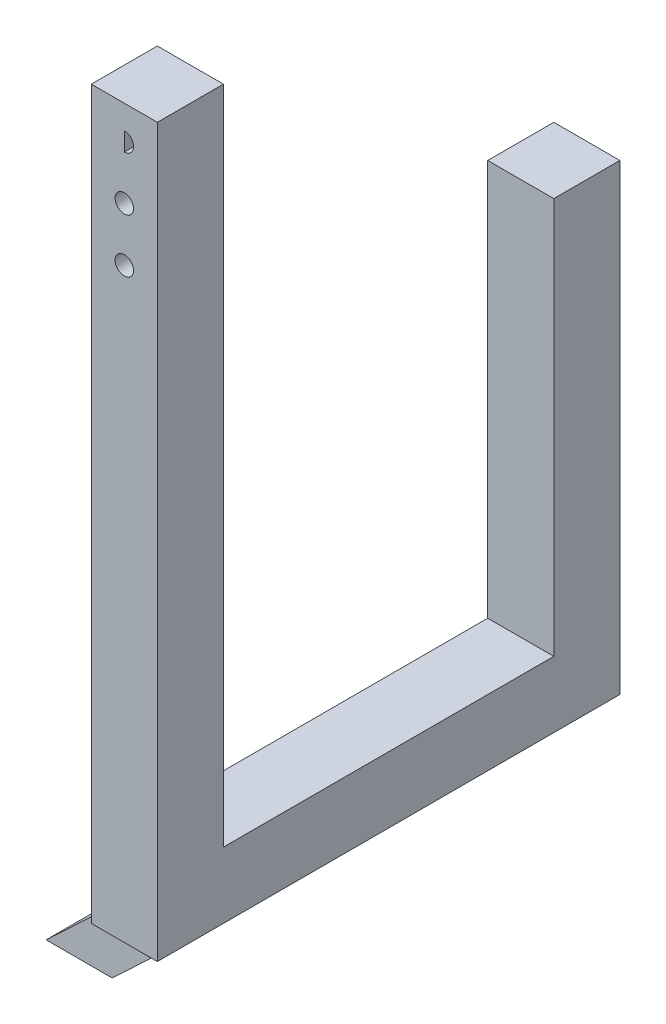
SolidWorks part; units mm, degrees
ref_plane "Front Plane" through (0, 0, 0) normal (0, 0, 1) x (1, 0, 0)
ref_plane "Top Plane" through (0, 0, 0) normal (0, 1, 0) x (1, 0, 0)
ref_plane "Right Plane" through (0, 0, 0) normal (1, 0, 0) x (0, 0, -1)
sketch "Sketch1" plane through (0, 0, 0) normal (0, 0, 1) x (1, 0, 0)
  line L1 (0, 0) -> (12.7, 0)
  line L2 (0, 0) -> (0, 139.7)
  line L3 (0, 139.7) -> (12.7, 139.7)
  line L4 (12.7, 0) -> (12.7, 139.7)
  dimension "D1" = 12.7
  dimension "D2" = 139.7
extrude "Boss-Extrude1" add sketch "Sketch1" along normal blind 12.7 contours L2 L1 L4 L3
sketch "Sketch2" plane through (0, 0, 0) normal (-1, 0, 0) x (0, 0, 1)
  line L1 (0, 0) -> (-63.5, 0)
  line L2 (0, 0) -> (0, 12.7)
  line L3 (0, 12.7) -> (-63.5, 12.7)
  line L4 (-63.5, 0) -> (-63.5, 12.7)
  dimension "D1" = 63.5
  dimension "D2" = 12.7
extrude "Boss-Extrude2" add sketch "Sketch2" against normal blind 12.7 contours L2 L1 L4 L3
sketch "Sketch3" plane through (0, 0, 0) normal (-1, 0, 0) x (0, 0, 1)
  line L1 (-63.5, 0) -> (-76.2, 0)
  line L2 (-63.5, 0) -> (-63.5, 88.9)
  line L3 (-63.5, 88.9) -> (-76.2, 88.9)
  line L4 (-76.2, 0) -> (-76.2, 88.9)
  dimension "D1" = 12.7
  dimension "D2" = 88.9
extrude "Boss-Extrude3" add sketch "Sketch3" against normal blind 12.7
sketch "Sketch4" plane through (0, 0, 12.7) normal (0, 0, 1) x (1, 0, 0)
  line L0 (12.7, 0) -> (39.4531, -27.1272)
  line L1 (39.4531, -27.1272) -> (26.7531, -27.1272)
  line L2 (26.7531, -27.1272) -> (0, 0)
  line L3 (0, 0) -> (12.7, 0)
  dimension "D1" = 38.1
  dimension "D2" = 38.1
  dimension "D3" = 12.7
sketch "Sketch6" plane through (0, 0, 12.7) normal (0, 0, 1) x (1, 0, 0)
  line L0 (6.35, 139.7) -> (6.35, 133.35)
  line L1 (0, 139.7) -> (12.7, 139.7) construction
  line L2 (6.35, 139.7) -> (6.35, 112.7125)
  line L3 (6.35, 133.35) -> (6.35, 112.7125)
  circle A0 centre (6.35, 133.35) radius 1.778
  circle A1 centre (6.35, 112.7125) radius 1.778
  circle A2 centre (6.35, 123.0312) radius 1.778
  dimension "D2" = 3.556
  dimension "D4" = 3.556
  dimension "D5" = 3.556
  dimension "D1" = 6.35
  dimension "D3" = 26.9875
extrude "Cut-Extrude1" cut sketch "Sketch6" against normal through all
sketch "Sketch7" plane through (0, 0, 12.7) normal (0, 0, 1) x (1, 0, 0)
  line L0 (0, 0) -> (-27.7296, -26.1281)
  line L1 (-27.7296, -26.1281) -> (-15.0296, -26.1281)
  line L2 (-15.0296, -26.1281) -> (12.7, 0)
  line L3 (12.7, 0) -> (0, 0)
  dimension "D1" = 38.1
  dimension "D2" = 38.1
  dimension "D3" = 12.7
extrude "Boss-Extrude7" add sketch "Sketch7" against normal blind 12.7 from offset 19.05 offset against normal yes
sketch "Sketch10" plane through (0, 0, -19.05) normal (0, 0, -1) x (-1, 0, 0)
  line L0 (-12.7, 0) -> (15.0296, -26.1281)
  line L1 (15.0296, -26.1281) -> (27.7296, -26.1281)
  line L2 (27.7296, -26.1281) -> (0, 0)
  line L3 (0, 0) -> (-12.7, 0)
extrude "Boss-Extrude8" add sketch "Sketch10" along normal blind 12.7 from offset 44.45
